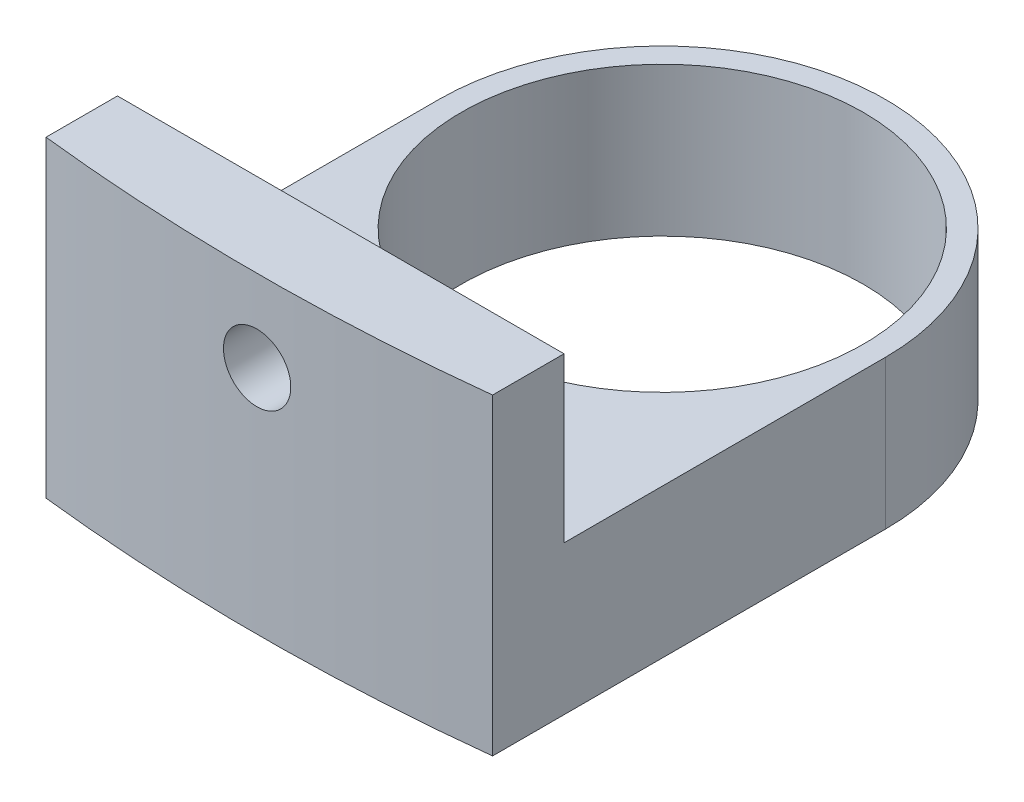
SolidWorks part; units mm, degrees
material "6061-T6 (SS)"
ref_plane "Front Plane" through (0, 0, 0) normal (0, 0, 1) x (1, 0, 0)
ref_plane "Top Plane" through (0, 0, 0) normal (0, 1, 0) x (1, 0, 0)
ref_plane "Right Plane" through (0, 0, 0) normal (1, 0, 0) x (0, 0, -1)
sketch "Sketch2" plane through (0, 0, 0) normal (0, 1, 0) x (1, 0, 0)
  circle A0 centre (0, 0) radius 8.5725
  circle A1 centre (0, 0) radius 9.525
  dimension "D1" = 17.145
  dimension "D2" = 19.05
extrude "Boss-Extrude1" add sketch "Sketch2" along normal mid plane 6.35
sketch "Sketch3" plane through (0, 0, 0) normal (0, 1, 0) x (1, 0, 0)
  line L0 (-9.525, 0) -> (-9.525, -16.764)
  line L2 (9.525, -16.764) -> (9.525, 0)
  circle A0 centre (0, 0) radius 9.525 construction
  arc A1 (9.525, 0) -> (-9.525, 0) centre (0, 0) cw
  arc A2 (-9.525, -16.764) -> (9.525, -16.764) centre (0, 68.4302) ccw
  point P10 (0, 0)
  point P11 (0, 0)
  dimension "D1" = 16.764
  dimension "D2" = 85.725
extrude "Boss-Extrude2" add sketch "Sketch3" along normal mid plane 6.35
sketch "Sketch4" plane through (0, 0, 0) normal (0, 1, 0) x (1, 0, 0)
  line L0 (-9.525, -16.764) -> (-9.525, -13.716)
  line L1 (-9.525, 0) -> (-9.525, -16.764) construction
  line L2 (-9.525, -13.716) -> (9.525, -13.716)
  line L3 (9.525, -16.764) -> (9.525, 0) construction
  line L4 (9.525, -13.716) -> (9.525, -16.764)
  arc A0 (-9.525, -16.764) -> (9.525, -16.764) centre (0, 68.4302) ccw
  dimension "D1" = 3.048
extrude "Boss-Extrude3" add sketch "Sketch4" along normal blind 10.16
sketch "Sketch5" plane through (0, 0, 13.716) normal (0, 0, -1) x (-1, 0, 0)
  circle A0 centre (0, 6.6675) radius 1.4351
  dimension "D1" = 2.8702
extrude "Cut-Extrude1" cut sketch "Sketch5" against normal blind 19.05
